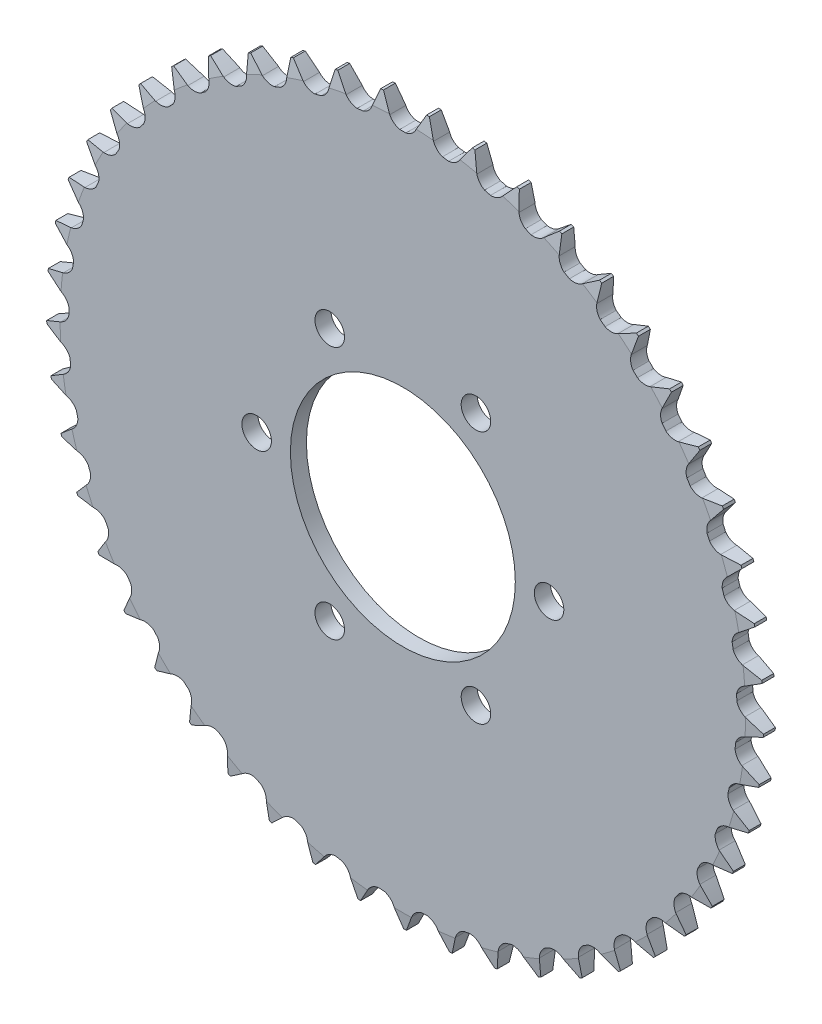
SolidWorks part; units mm, degrees
material "7075-T6 (SN)"
ref_plane "Płaszczyzna XY" through (0, 0, 0) normal (0, 0, 1) x (1, 0, 0)
ref_plane "Płaszczyzna XZ" through (0, 0, 0) normal (0, 1, 0) x (1, 0, 0)
ref_plane "Płaszczyzna YZ" through (0, 0, 0) normal (1, 0, 0) x (0, 0, -1)
sketch "Szkic1" plane through (0, 0, 0) normal (0, 0, 1) x (1, 0, 0)
  line L0 (0, 0) -> (0, 138.6783) construction
  line L1 (0, 0) -> (-8.4491, 131.602) construction
  line L2 (0, 0) -> (8.4966, 132.3418) construction
  line L3 (0, 123.885) -> (-127.785, 60.1738) construction
  line L4 (0, 123.885) -> (35.4084, 106.231) construction
  line L5 (8.169, 127.238) -> (7.612, 118.5634)
  line L6 (-8.169, 127.238) -> (-7.612, 118.5634)
  circle A0 centre (0, 0) radius 118.8075
  circle A1 centre (0, 0) radius 123.885
  circle A2 centre (0, 0) radius 127.5
  circle A3 centre (0, 123.885) radius 5.2
  arc A4 (-7.6915, 127.2678) -> (-4.6537, 121.5648) centre (-112.0458, 68.021) cw
  arc A5 (4.6537, 121.5648) -> (7.6915, 127.2678) centre (112.0458, 68.021) cw
  dimension "D1" = 237.615
  dimension "D2" = 247.77
  dimension "D3" = 255
  dimension "D6" = 10.4
  dimension "D9" = 120
  dimension "D4" = 3.673
  dimension "D5" = 7.347
  dimension "D7" = 127
  dimension "D8" = 63.5
extrude "Dodanie-wyciągnięcie1" add sketch "Szkic1" along normal blind 5.7 contours A4 A1 L6 A0 A3 | A5 A3 A0 L5 A1 | A5 A1 L5 A2 | A4 A2 L6 A1 | A3 A0
pattern_circular "Szyk kołowy1" count 49 over 360 about axis through (0, 0, 0) along (0, 0, 1) of "Dodanie-wyciągnięcie1"
ref_plane "Płaszczyzna1" through (0, 0, 15.7) normal (0, 0, 1) x (1, 0, 0)
sketch "Szkic3" plane through (0, 0, 15.7) normal (0, 0, 1) x (1, 0, 0)
  circle A0 centre (0, 0) radius 52
  circle A1 centre (52, 0) radius 5.25
  dimension "D1" = 104
  dimension "D2" = 10.5
extrude "Wytnij-wyciągnięcie3" cut sketch "Szkic3" against normal blind 25.7 contours A1
ref_plane "Płaszczyzna2" through (0, 0, 5.7) normal (0, 0, 1) x (1, 0, 0)
sketch "Szkic4" plane through (0, 0, 5.7) normal (0, 0, 1) x (1, 0, 0)
  circle A0 centre (0, 0) radius 121.885
  dimension "D1" = 243.77
extrude "Wytnij-wyciągnięcie4" cut sketch "Szkic4" against normal blind 35.7 draft 82 flip side to cut contours A0
sketch "Szkic5" plane through (0, 0, 0) normal (0, 0, -1) x (-1, 0, 0)
  circle A0 centre (0, 0) radius 121.885
  dimension "D1" = 243.77
extrude "Wytnij-wyciągnięcie5" cut sketch "Szkic5" against normal blind 25.7 draft 83 flip side to cut contours A0
pattern_circular "Szyk kołowy2" count 6 over 360 about axis through (0, 0, 0) along (0, 0, 1) of "Wytnij-wyciągnięcie3"
sketch "Szkic6" plane through (0, 0, 0) normal (0, 0, -1) x (-1, 0, 0)
  circle A0 centre (0, 0) radius 40
  dimension "D1" = 80
extrude "Wytnij-wyciągnięcie6" cut sketch "Szkic6" against normal blind 10
ref_plane "Płaszczyzna3" through (0, 0, 5.7) normal (0, 0, 1) x (1, 0, 0)
ref_plane "Płaszczyzna4" through (0, 0, -4.325) normal (0, 0, -1) x (-1, 0, 0)
equation "\"df\"= 237.615mm"
equation "\"D1@Szkic1\"= \"df\""
equation "\"d\"= 247.77mm"
equation "\"D2@Szkic1\"=\"d\""
equation "\"da\"= 255"
equation "\"D3@Szkic1\"= \"da\""
equation "\"alfa\"= 127stopnie"
equation "\"D4@Szkic1\"= 360 / ( 2 * \"z\" )"
equation "\"z\"= 49"
equation "\"D5@Szkic1\"= 360 / \"z\""
equation "\"ri\"= 5.2"
equation "\"D6@Szkic1\"= \"ri\" * 2"
equation "\"D7@Szkic1\"= \"alfa\""
equation "\"D8@Szkic1\"= \"alfa\" / 2"
equation "\"re\"= 120"
equation "\"D9@Szkic1\"=\"re\""
equation "\"D1@Szyk kołowy1\"= \"z\""
equation "\"D1@Szkic5\"= \"d\" - 4"
equation "\"D1@Szkic4\"= \"d\" - 4"
